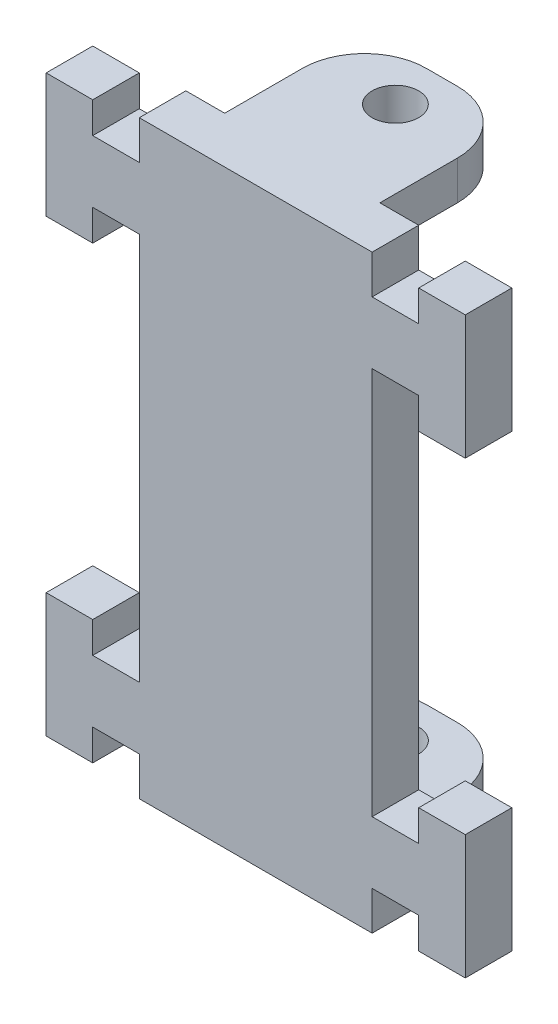
SolidWorks part; units mm, degrees
ref_plane "정면" through (0, 0, 0) normal (0, 0, 1) x (1, 0, 0)
ref_plane "윗면" through (0, 0, 0) normal (0, 1, 0) x (1, 0, 0)
ref_plane "우측면" through (0, 0, 0) normal (1, 0, 0) x (0, 0, -1)
sketch "스케치1" plane through (0, 0, 0) normal (0, 0, 1) x (1, 0, 0)
  line L0 (0, 0) -> (-13.1641, 0) construction
  line L1 (-7.5, 19) -> (7.5, 19)
  line L2 (-7.5, 19) -> (-7.5, -19)
  line L3 (-7.5, -19) -> (7.5, -19)
  line L4 (7.5, 19) -> (7.5, -19)
  line L5 (-7.5, 19) -> (7.5, -19) construction
  line L6 (-7.5, -19) -> (7.5, 19) construction
  point P0 (0, 0)
  dimension "D1" = 15
  dimension "D2" = 38
extrude "보스-돌출1" add sketch "스케치1" along normal blind 3
sketch "스케치5" plane through (0, 0, 0) normal (0, 0, -1) x (-1, 0, 0)
  line L0 (-7.5, 16.5) -> (-10.5, 16.5)
  line L2 (-10.5, 16.5) -> (-10.5, 18.5)
  line L3 (-10.5, 18.5) -> (-13.5, 18.5)
  line L4 (-13.5, 18.5) -> (-13.5, 10.5)
  line L5 (-13.5, 10.5) -> (-10.5, 10.5)
  line L6 (-10.5, 10.5) -> (-10.5, 12.5)
  line L7 (-10.5, 12.5) -> (-7.5, 12.5)
  line L8 (-7.5, 16.5) -> (-7.5, 12.5)
  line L9 (-7.5, 14.5) -> (-13.1442, 14.5) construction
  line L11 (0, 0) -> (0, 7.6378) construction
  line L12 (0, 0) -> (17.2492, 0) construction
  line L13 (7.5, 14.5) -> (13.1442, 14.5) construction
  line L14 (7.5, 16.5) -> (7.5, 12.5)
  line L15 (10.5, 12.5) -> (7.5, 12.5)
  line L16 (10.5, 10.5) -> (10.5, 12.5)
  line L17 (13.5, 10.5) -> (10.5, 10.5)
  line L18 (13.5, 18.5) -> (13.5, 10.5)
  line L19 (10.5, 18.5) -> (13.5, 18.5)
  line L20 (10.5, 16.5) -> (10.5, 18.5)
  line L21 (7.5, 16.5) -> (10.5, 16.5)
  line L22 (7.5, -14.5) -> (13.1442, -14.5) construction
  line L23 (-7.5, -14.5) -> (-13.1442, -14.5) construction
  line L24 (7.5, -16.5) -> (10.5, -16.5)
  line L25 (10.5, -16.5) -> (10.5, -18.5)
  line L26 (10.5, -18.5) -> (13.5, -18.5)
  line L27 (13.5, -18.5) -> (13.5, -10.5)
  line L28 (13.5, -10.5) -> (10.5, -10.5)
  line L29 (10.5, -10.5) -> (10.5, -12.5)
  line L30 (10.5, -12.5) -> (7.5, -12.5)
  line L31 (7.5, -16.5) -> (7.5, -12.5)
  line L32 (-7.5, -16.5) -> (-7.5, -12.5)
  line L33 (-10.5, -12.5) -> (-7.5, -12.5)
  line L34 (-10.5, -10.5) -> (-10.5, -12.5)
  line L35 (-13.5, -10.5) -> (-10.5, -10.5)
  line L36 (-13.5, -18.5) -> (-13.5, -10.5)
  line L37 (-10.5, -18.5) -> (-13.5, -18.5)
  line L38 (-10.5, -16.5) -> (-10.5, -18.5)
  line L39 (-7.5, -16.5) -> (-10.5, -16.5)
  line L40 (-7.5, -19) -> (-7.5, 19) construction
  dimension "D1" = 8
  dimension "D2" = 4
  dimension "D3" = 10.5
  dimension "D4" = 3
  dimension "D5" = 3
extrude "보스-돌출4" add sketch "스케치5" against normal blind 3
sketch "스케치6" plane through (0, 0, 0) normal (0, 0, -1) x (-1, 0, 0)
  line L0 (-7.5, 19) -> (7.5, 19) construction
  line L1 (-5, 19) -> (5, 19)
  line L2 (-5, 19) -> (-5, 16.5)
  line L3 (-5, 16.5) -> (5, 16.5)
  line L4 (5, 19) -> (5, 16.5)
  line L10 (-7.5, 16.5) -> (-7.5, 19) construction
  line L11 (7.5, 19) -> (7.5, 16.5) construction
  line L12 (0, 0) -> (6.2756, 0) construction
  line L14 (5, -19) -> (5, -16.5)
  line L15 (-5, -16.5) -> (5, -16.5)
  line L16 (-5, -19) -> (-5, -16.5)
  line L17 (-5, -19) -> (5, -19)
  dimension "D1" = 2.5
  dimension "D2" = 2.5
  dimension "D3" = 2.5
extrude "보스-돌출5" add sketch "스케치6" along normal blind 9
hole_wizard "Ø3.0 (3) 지름 구멍1" positions "스케치7" profile "스케치8" hole size "Ø3.0" standard "ISO" end condition through all
sketch "스케치7" plane through (0, 19, 0) normal (0, 1, 0) x (1, 0, 0)
  line L1 (-7.5, -3) -> (-7.5, 0) construction
  line L2 (-5, 9) -> (5, 9) construction
  point P0 (0, 6)
  dimension "D1" = 7.5
  dimension "D2" = 3
sketch "스케치8" plane through (0, 19, -6) normal (1, 0, 0) x (0, 0, 1)
  line L0 (0, 0) -> (0, 38)
  line L1 (0, 38) -> (1.5, 38)
  line L2 (1.5, 38) -> (1.5, 0)
  line L5 (1.5, 0) -> (0, 0)
  line L11 (0, -6.35) -> (0, 107.95) construction
  dimension "관통 구멍 지름" = 3
  dimension "관통 구멍 깊이" = 38
fillet "필렛1" radius 4 4 edges at (-5, -17.75, -9) (5, -17.75, -9) (-5, 17.75, -9) (5, 17.75, -9)
